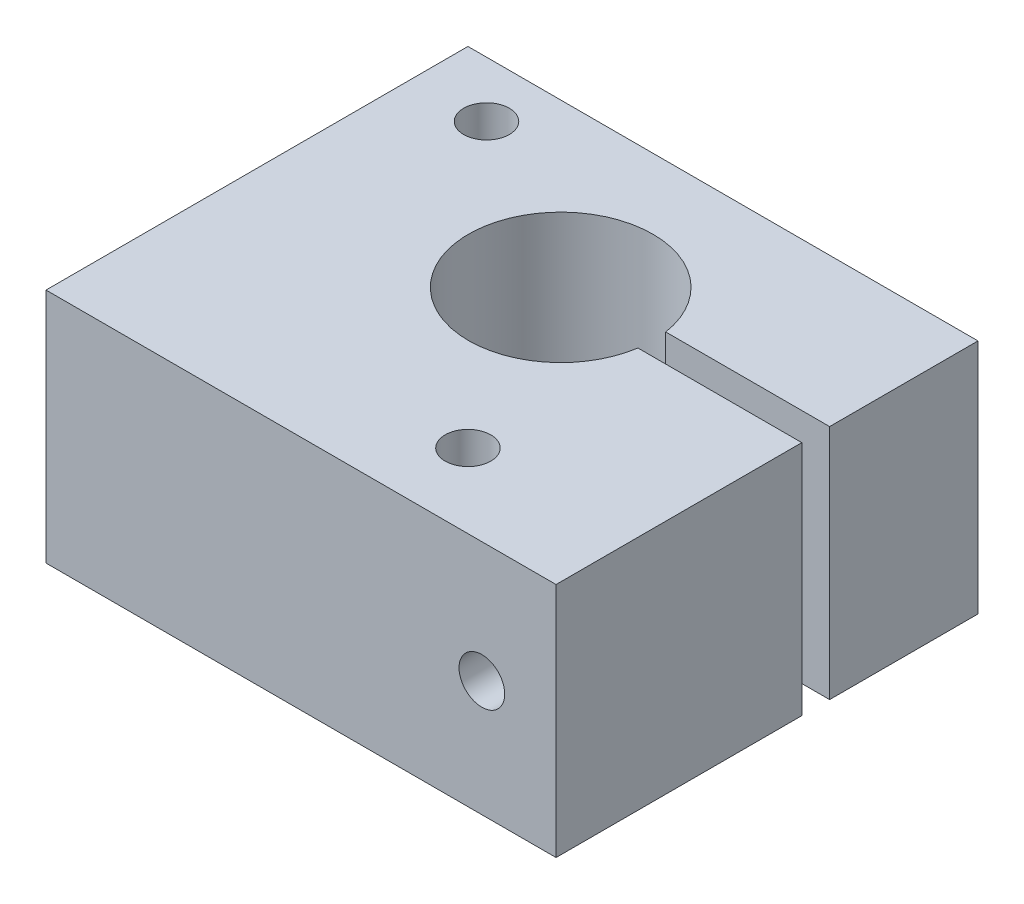
SolidWorks part; units mm, degrees
ref_plane "Front Plane" through (0, 0, 0) normal (0, 0, 1) x (1, 0, 0)
ref_plane "Top Plane" through (0, 0, 0) normal (0, 1, 0) x (1, 0, 0)
ref_plane "Right Plane" through (0, 0, 0) normal (1, 0, 0) x (0, 0, -1)
sketch "Sketch1" plane through (0, 0, 0) normal (0, 1, 0) x (1, 0, 0)
  line L1 (-13.97, -11.557) -> (13.97, -11.557)
  line L2 (-13.97, -11.557) -> (-13.97, 11.557)
  line L3 (-13.97, 11.557) -> (13.97, 11.557)
  line L4 (13.97, -11.557) -> (13.97, 11.557)
  line L5 (-13.97, -11.557) -> (13.97, 11.557) construction
  line L6 (-13.97, 11.557) -> (13.97, -11.557) construction
  point P0 (0, 0)
  dimension "D1" = 27.94
  dimension "D2" = 23.114
extrude "Boss-Extrude1" add sketch "Sketch1" along normal blind 12.954
sketch "Sketch2" plane through (0, 12.954, 0) normal (0, 1, 0) x (1, 0, 0)
  line L0 (-13.97, 11.557) -> (-13.97, -11.557) construction
  line L1 (13.97, 11.557) -> (-13.97, 11.557) construction
  circle A0 centre (0, 2.667) radius 5.05
  dimension "D1" = 13.97
  dimension "D2" = 8.89
extrude "Cut-Extrude1" cut sketch "Sketch2" against normal through all
sketch "Sketch3" plane through (0, 12.954, 0) normal (0, 1, 0) x (1, 0, 0)
  line L0 (13.97, -11.557) -> (13.97, 11.557) construction
  line L1 (0, 3.429) -> (13.97, 3.429)
  line L2 (0, 3.429) -> (0, 1.905)
  line L3 (0, 1.905) -> (13.97, 1.905)
  line L4 (13.97, 3.429) -> (13.97, 1.905)
  circle A0 centre (0, 2.667) radius 5.05 construction
  dimension "D1" = 1.524
  dimension "D2" = 0
  dimension "D3" = 0
  dimension "D4" = 0.762
extrude "Cut-Extrude2" cut sketch "Sketch3" against normal through all
sketch "Sketch4" plane through (0, 12.954, 0) normal (0, 1, 0) x (1, 0, 0)
  line L0 (-13.97, 11.557) -> (-13.97, -11.557) construction
  line L1 (13.97, 11.557) -> (-13.97, 11.557) construction
  line L2 (13.97, -11.557) -> (13.97, 1.905) construction
  line L3 (-13.97, -11.557) -> (13.97, -11.557) construction
  circle A0 centre (-9.906, 8.509) radius 1.25
  circle A1 centre (5.08, -7.493) radius 1.25
  dimension "D1" = 4.064
  dimension "D2" = 3.048
  dimension "D3" = 8.89
  dimension "D4" = 4.064
extrude "Cut-Extrude3" cut sketch "Sketch4" against normal through all
sketch "Sketch5" plane through (0, 0, -11.557) normal (0, 0, -1) x (-1, 0, 0)
  line L0 (-13.97, 12.954) -> (-13.97, 0) construction
  line L1 (-13.97, 0) -> (13.97, 0) construction
  circle A0 centre (-9.906, 6.35) radius 3.048
  dimension "D2" = 6.35
  dimension "D3" = 6.096
  dimension "D1" = 4.064
extrude "Cut-Extrude4" cut sketch "Sketch5" against normal blind 4.318
sketch "Sketch6" plane through (0, 0, -7.239) normal (0, 0, -1) x (-1, 0, 0)
  circle A0 centre (-9.906, 6.35) radius 1.7
extrude "Cut-Extrude5" cut sketch "Sketch6" against normal up to next
sketch "Sketch7" plane through (0, 0, -7.239) normal (0, 0, -1) x (-1, 0, 0)
  circle A0 centre (-9.906, 6.35) radius 1.25
extrude "Cut-Extrude6" cut sketch "Sketch7" against normal through all
